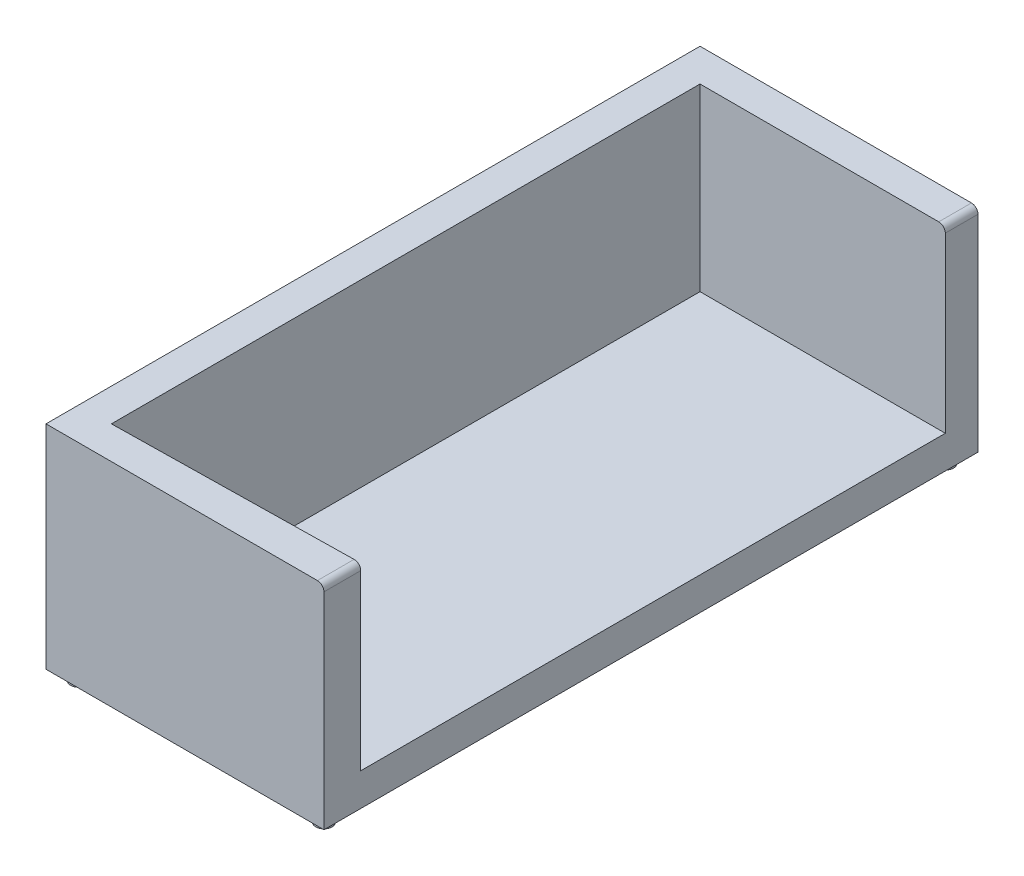
SolidWorks part; units mm, degrees
ref_plane "Front Plane" through (0, 0, 0) normal (0, 0, 1) x (1, 0, 0)
ref_plane "Top Plane" through (0, 0, 0) normal (0, 1, 0) x (1, 0, 0)
ref_plane "Right Plane" through (0, 0, 0) normal (1, 0, 0) x (0, 0, -1)
sketch "Sketch1" plane through (0, 0, 0) normal (0, 0, 1) x (1, 0, 0)
  line L1 (-425, 270.9651) -> (405, 270.9651)
  line L2 (-425, 270.9651) -> (-425, -379.0349)
  line L3 (-425, -379.0349) -> (425, -379.0349)
  line L4 (425, 250.9651) -> (425, -379.0349)
  line L5 (-425, 270.9651) -> (425, -379.0349) construction
  line L6 (-425, -379.0349) -> (425, 270.9651) construction
  arc A0 (405, 270.9651) -> (425, 250.9651) centre (405, 250.9651) cw
  point P0 (0, 0)
  dimension "D3" = 20
  dimension "D1" = 850
  dimension "D2" = 650
extrude "Boss-Extrude1" add sketch "Sketch1" along normal blind 2000
sketch "Sketch3" plane through (0, 270.9651, 0) normal (0, 1, 0) x (1, 0, 0)
  line L1 (-325, -100) -> (425, -100)
  line L3 (-325, -100) -> (-325, -1900)
  line L4 (-325, -1900) -> (425, -1887.575)
  line L5 (425, -1887.575) -> (425, -100)
extrude "Cut-Extrude1" cut sketch "Sketch3" against normal blind 550
sketch "Sketch4" plane through (0, -379.0349, 0) normal (0, -1, 0) x (-1, 0, 0)
  line L0 (425, -2000) -> (425, 0) construction
  line L1 (425, -2000) -> (-425, -2000) construction
  line L2 (-425, -2000) -> (-425, 0) construction
  line L3 (425, 0) -> (-425, 0) construction
  circle A0 centre (375, -1950) radius 25
  circle A1 centre (-375, -1950) radius 25
  circle A2 centre (375, -50) radius 25
  circle A3 centre (-375, -50) radius 25
  dimension "D1" = 50
  dimension "D6" = 50
  dimension "D9" = 50
  dimension "D12" = 50
  dimension "D2" = 50
  dimension "D3" = 50
  dimension "D4" = 50
  dimension "D5" = 50
  dimension "D7" = 50
  dimension "D8" = 50
  dimension "D10" = 50
  dimension "D11" = 50
extrude "Boss-Extrude2" add sketch "Sketch4" along normal blind 30
sketch "Sketch6" plane through (0, -379.0349, 0) normal (0, -1, 0) x (1, 0, 0)
  line L0 (-375, 1950) -> (375, 1950)
